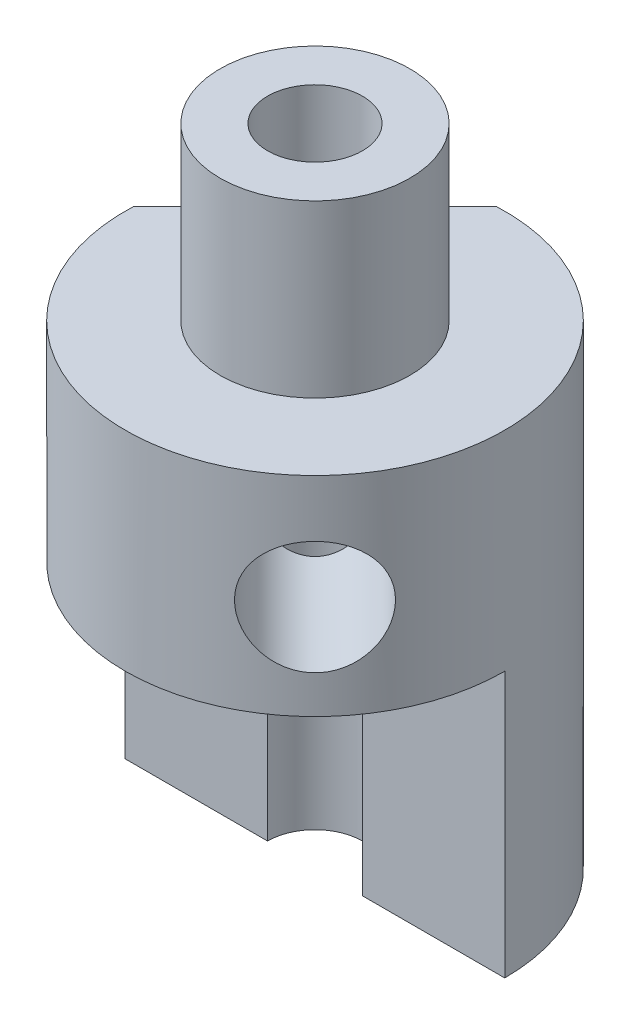
SolidWorks part; units mm, degrees
material "2024-T4"
ref_plane "Спереди" through (0, 0, 0) normal (0, 0, 1) x (1, 0, 0)
ref_plane "Сверху" through (0, 0, 0) normal (0, 1, 0) x (1, 0, 0)
ref_plane "Справа" through (0, 0, 0) normal (1, 0, 0) x (0, 0, -1)
sketch "Эскиз1" plane through (0, 0, 0) normal (1, 0, 0) x (0, 0, -1)
  line L0 (2.5, -4.5) -> (2.5, 0)
  line L3 (5, -4.5) -> (5, -17)
  line L4 (5, -17) -> (1.25, -17)
  line L5 (1.25, -17) -> (1.25, 0)
  line L6 (2.5, -4.5) -> (5, -4.5)
  line L7 (2.5, 0) -> (1.25, 0)
  line L8 (0, 0) -> (0, -17.5) construction
  dimension "D1" = 2.5
  dimension "D2" = 17
  dimension "D4" = 4.5
  dimension "D5" = 5
  dimension "D7" = 1.25
revolve "Повернуть1" add sketch "Эскиз1" angle 360 about L8
sketch "Эскиз2" plane through (0, -17, 0) normal (0, -1, 0) x (1, 0, 0)
  line L0 (-5, 0) -> (5, 0)
  circle A0 centre (0, 0) radius 5 construction
  circle M1 centre (0, 0) radius 5
extrude "Вырез-Вытянуть1" cut sketch "Эскиз2" against normal blind 7 contours L0 M1
sketch "Эскиз3" plane through (0, -17, 0) normal (0, -1, 0) x (1, 0, 0)
  line L0 (-4.9955, -0.2126) -> (-0.2126, -4.9955)
  line L1 (-5, 0) -> (-1.25, 0) construction
  arc A0 (-5, 0) -> (5, 0) centre (0, 0) ccw construction
  arc M1 (-5, 0) -> (5, 0) centre (0, 0) ccw
  dimension "D1" = 45
  dimension "D2" = 3.6827
extrude "Вырез-Вытянуть2" cut sketch "Эскиз3" against normal through all contours L0 M1
ref_plane "Плоскость2" through (-2.5, 0, 2.5) normal (0.7071, 0, -0.7071) x (-0.7071, 0, -0.7071)
sketch "Эскиз5" plane through (-7.7081, 0, 2.5) normal (0.7071, 0, 0.7071) x (0.7071, 0, -0.7071)
  line L0 (12.2182, -4.5) -> (2.2182, -4.5) construction
  circle A0 centre (7.2182, -7.5) radius 1.5
  dimension "D1" = 3
  dimension "D2" = 3
extrude "Вырез-Вытянуть3" cut sketch "Эскиз5" against normal through all and the other way up to next
